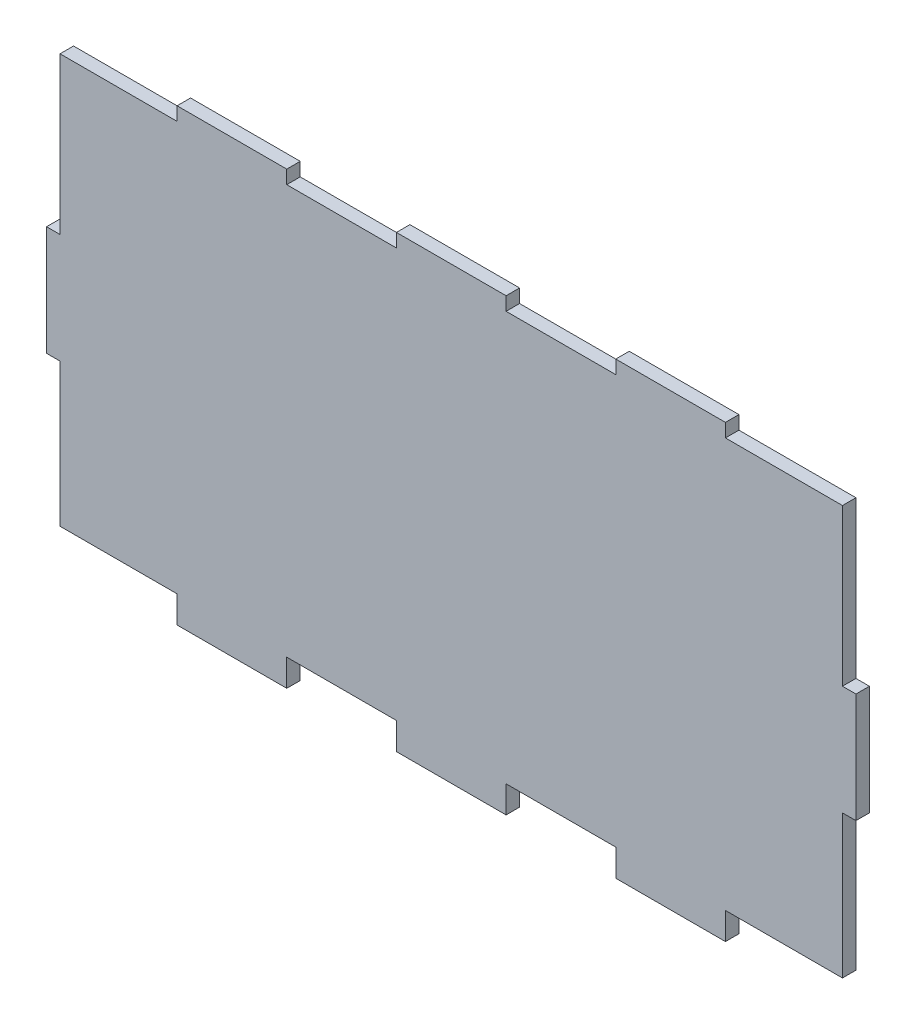
SolidWorks part; units mm, degrees
ref_plane "Alzado" through (0, 0, 0) normal (0, 0, 1) x (1, 0, 0)
ref_plane "Planta" through (0, 0, 0) normal (0, 1, 0) x (1, 0, 0)
ref_plane "Vista lateral" through (0, 0, 0) normal (1, 0, 0) x (0, 0, -1)
sketch "Model" plane through (0, 0, 0) normal (0, 0, 1) x (1, 0, 0)
  line L0 (289, 97) -> (289, 62.195)
  line L1 (289, 62.195) -> (286, 62.195)
  line L2 (286, 62.195) -> (286, 37.805)
  line L3 (286, 37.805) -> (289, 37.805)
  line L4 (289, 37.805) -> (289, 13.415)
  line L5 (289, 13.415) -> (289, 3)
  line L6 (289, 3) -> (315.025, 3)
  line L7 (315.025, 3) -> (315.025, 0)
  line L8 (315.025, 0) -> (339.415, 0)
  line L9 (339.415, 0) -> (339.415, 3)
  line L10 (339.415, 3) -> (363.805, 3)
  line L11 (363.805, 3) -> (363.805, 0)
  line L12 (363.805, 0) -> (388.195, 0)
  line L13 (388.195, 0) -> (388.195, 3)
  line L14 (388.195, 3) -> (412.585, 3)
  line L15 (412.585, 3) -> (412.585, 0)
  line L16 (412.585, 0) -> (436.975, 0)
  line L17 (436.975, 0) -> (436.975, 3)
  line L18 (436.975, 3) -> (461.365, 3)
  line L19 (461.365, 3) -> (463, 3)
  line L20 (463, 3) -> (463, 37.805)
  line L21 (463, 37.805) -> (466, 37.805)
  line L22 (466, 37.805) -> (466, 62.195)
  line L23 (466, 62.195) -> (463, 62.195)
  line L24 (463, 62.195) -> (463, 86.585)
  line L25 (463, 86.585) -> (463, 97)
  line L26 (463, 97) -> (436.975, 97)
  line L27 (436.975, 97) -> (436.975, 100)
  line L28 (436.975, 100) -> (412.585, 100)
  line L29 (412.585, 100) -> (412.585, 97)
  line L30 (412.585, 97) -> (388.195, 97)
  line L31 (388.195, 97) -> (388.195, 100)
  line L32 (388.195, 100) -> (363.805, 100)
  line L33 (363.805, 100) -> (363.805, 97)
  line L34 (363.805, 97) -> (339.415, 97)
  line L35 (339.415, 97) -> (339.415, 100)
  line L36 (339.415, 100) -> (315.025, 100)
  line L37 (315.025, 100) -> (315.025, 97)
  line L38 (315.025, 97) -> (290.635, 97)
  line L39 (290.635, 97) -> (289, 97)
extrude "Saliente-Extruir1" add sketch "Model" along normal blind 3
sketch "Croquis1" plane through (0, 0, 3) normal (0, 0, 1) x (1, 0, 0)
  line L0 (289, 37.805) -> (289, 3) construction
  line L1 (315.025, 3) -> (289, 3)
  line L2 (315.025, 3) -> (315.025, 6)
  line L3 (315.025, 6) -> (289, 6)
  line L4 (289, 3) -> (289, 6)
  line L5 (463, 3) -> (463, 37.805) construction
  line L6 (339.415, 3) -> (363.805, 3)
  line L7 (339.415, 3) -> (339.415, 6)
  line L8 (339.415, 6) -> (363.805, 6)
  line L9 (363.805, 3) -> (363.805, 6)
  line L10 (388.195, 3) -> (412.585, 3)
  line L11 (388.195, 3) -> (388.195, 6)
  line L12 (388.195, 6) -> (412.585, 6)
  line L13 (412.585, 3) -> (412.585, 6)
  line L14 (436.975, 3) -> (463, 3)
  line L15 (436.975, 3) -> (436.975, 6)
  line L16 (436.975, 6) -> (463, 6)
  line L17 (463, 3) -> (463, 6)
  line L18 (363.805, 3) -> (363.805, 0) construction
  line L19 (412.585, 3) -> (412.585, 0) construction
  dimension "D1" = 3
extrude "Cortar-Extruir1" cut sketch "Croquis1" against normal blind 3
